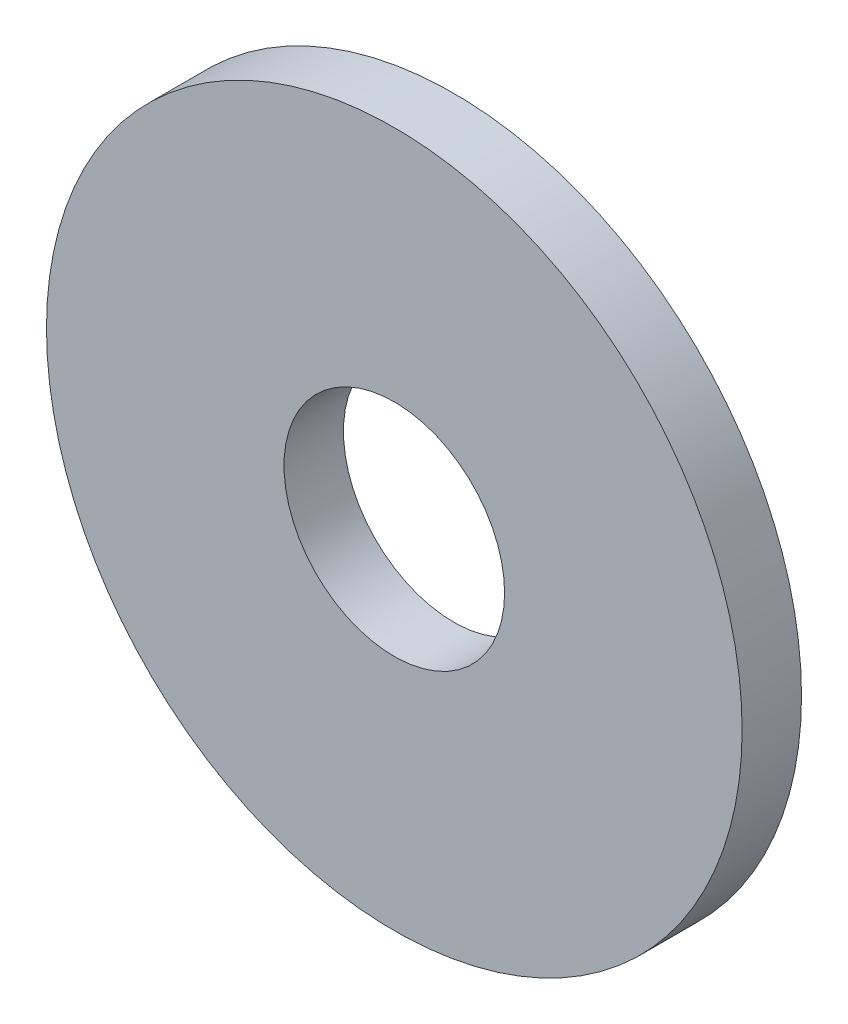
SolidWorks part; units mm, degrees
ref_plane "Přední rovina" through (0, 0, 0) normal (0, 0, 1) x (1, 0, 0)
ref_plane "Horní rovina" through (0, 0, 0) normal (0, 1, 0) x (1, 0, 0)
ref_plane "Pravá rovina" through (0, 0, 0) normal (1, 0, 0) x (0, 0, -1)
sketch "Skica1" plane through (0, 0, 0) normal (0, 0, 1) x (1, 0, 0)
  circle A0 centre (0, 0) radius 5.2
  circle A1 centre (0, 0) radius 16.4
  dimension "D1" = 10.4
  dimension "D2" = 32.8
extrude "Přidat vysunutím1" add sketch "Skica1" along normal blind 2.8
